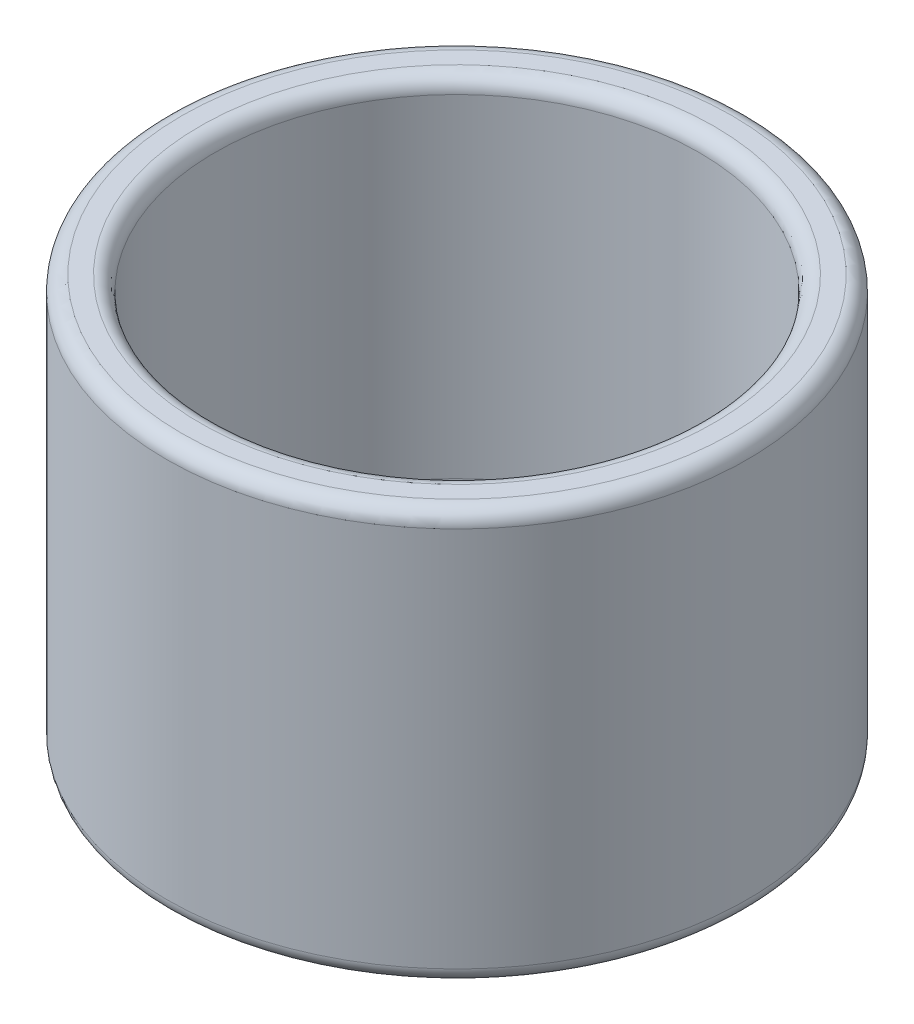
SolidWorks part; units mm, degrees
ref_plane "Front Plane" through (0, 0, 0) normal (0, 0, 1) x (1, 0, 0)
ref_plane "Top Plane" through (0, 0, 0) normal (0, 1, 0) x (1, 0, 0)
ref_plane "Right Plane" through (0, 0, 0) normal (1, 0, 0) x (0, 0, -1)
sketch "Sketch1" plane through (0, 0, 0) normal (0, 0, 1) x (1, 0, 0)
  line L0 (-15.24, 21.59) -> (-15.24, 0)
  line L1 (-15.24, 0) -> (0, 0)
  line L2 (0, 0) -> (0, 2.54) construction
  line L3 (0, 2.54) -> (-12.7, 2.54)
  line L4 (-12.7, 2.54) -> (-12.7, 21.59)
  line L5 (-12.7, 21.59) -> (-15.24, 21.59)
  line L6 (-15.24, 0) -> (-12.7, 2.54) construction
  line L7 (0, 0) -> (0, 2.54)
  point P5 (-15.24, 24.765)
  dimension "D1" = 2.54
  dimension "D2" = 25.4
  dimension "D3" = 19.05
  dimension "D4" = 45
revolve "Revolve1" add sketch "Sketch1" angle 360 about L7
fillet "Fillet1" radius 0.7937 4 edges at (0, 0, -15.24) (0, 2.54, -12.7) (0, 21.59, -12.7) (0, 21.59, -15.24)
sketch "Sketch3" plane through (0, 2.54, 0) normal (0, 1, 0) x (1, 0, 0)
  point P0 (0, 0)
hole_wizard "CSK for #10 Flat Head Machine Screw (100)1" positions "3DSketch2" profile "Sketch4" countersink size "#10" standard "ANSI Inch" end condition through all
sketch3d "3DSketch2"
  point P0 (0, 2.54, 0)
sketch "Sketch4" plane through (0, 2.54, 0) normal (1, 0, 0) x (0, 0, 1)
  line L0 (0, 0) -> (0, 2.54)
  line L1 (0, 2.54) -> (2.5527, 2.54)
  line L2 (2.5527, 2.54) -> (2.5527, 1.9608)
  line L3 (2.5527, 1.9608) -> (4.8895, 0)
  line L5 (4.8895, 0) -> (0, 0)
  line L6 (-2.5527, 1.9608) -> (-4.8895, 0) construction
  line L11 (0, -6.35) -> (0, 107.95) construction
  dimension "Thru Hole Dia." = 5.1054
  dimension "Thru Hole Depth" = 2.54
  dimension "Near C'Sink Dia." = 9.779
  dimension "Near C'Sink Angle" = 100
